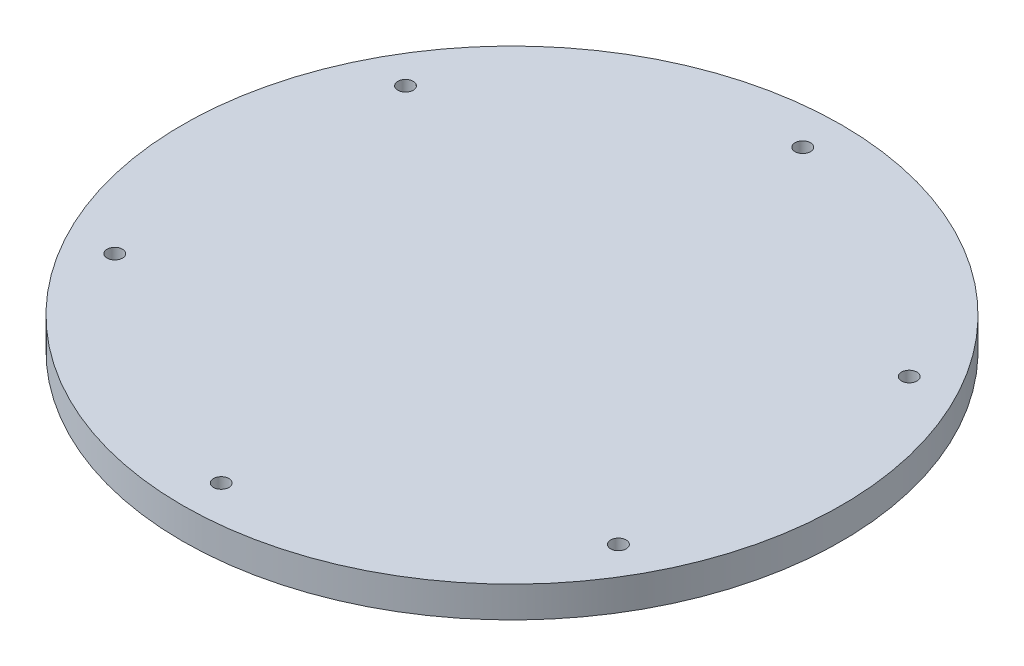
SolidWorks part; units mm, degrees
ref_plane "前视基准面" through (0, 0, 0) normal (0, 0, 1) x (1, 0, 0)
ref_plane "上视基准面" through (0, 0, 0) normal (0, 1, 0) x (1, 0, 0)
ref_plane "右视基准面" through (0, 0, 0) normal (1, 0, 0) x (0, 0, -1)
sketch "草图1" plane through (0, 0, 0) normal (0, 1, 0) x (1, 0, 0)
  circle A0 centre (0, 0) radius 85
  circle A1 centre (0, 0) radius 75
  circle A2 centre (0, -75) radius 2
  circle A3 centre (-64.9519, -37.5) radius 2
  circle A4 centre (-64.9519, 37.5) radius 2
  circle A5 centre (0, 75) radius 2
  circle A6 centre (64.9519, 37.5) radius 2
  circle A7 centre (64.9519, -37.5) radius 2
  point P18 (0, 0)
  dimension "D1" = 6
extrude "凸台-拉伸1" add sketch "草图1" along normal blind 8 contours A0
sketch "草图2" plane through (0, 8, 0) normal (0, 1, 0) x (1, 0, 0)
  circle A0 centre (0, 0) radius 75
  circle A1 centre (0, -75) radius 2
  circle A2 centre (-64.9519, -37.5) radius 2
  circle A3 centre (-64.9519, 37.5) radius 2
  circle A4 centre (0, 75) radius 2
  circle A5 centre (64.9519, 37.5) radius 2
  circle A6 centre (64.9519, -37.5) radius 2
  point P17 (0, 0)
  dimension "D1" = 6
extrude "切除-拉伸1" cut sketch "草图2" against normal through all contours A5 | A4 | A3 | A2 | A1 | A6
